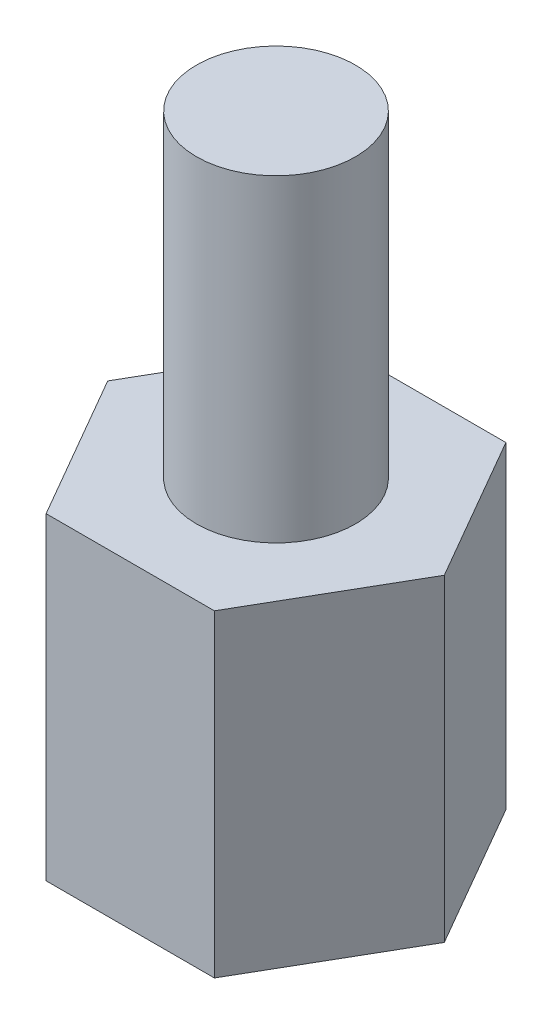
SolidWorks part; units mm, degrees
ref_plane "前视基准面" through (0, 0, 0) normal (0, 0, 1) x (1, 0, 0)
ref_plane "上视基准面" through (0, 0, 0) normal (0, 1, 0) x (1, 0, 0)
ref_plane "右视基准面" through (0, 0, 0) normal (1, 0, 0) x (0, 0, -1)
other "Configuration Table"
sketch "草图1" plane through (0, 0, 0) normal (0, 1, 0) x (1, 0, 0)
  line L1 (3.1754, 0) -> (1.5877, 2.75)
  line L2 (1.5877, 2.75) -> (-1.5877, 2.75)
  line L3 (-1.5877, 2.75) -> (-3.1754, 0)
  line L4 (-3.1754, 0) -> (-1.5877, -2.75)
  line L5 (-1.5877, -2.75) -> (1.5877, -2.75)
  line L6 (1.5877, -2.75) -> (3.1754, 0)
  circle A0 centre (0, 0) radius 2.75 construction
extrude "凸台-拉伸1" add sketch "草图1" along normal blind 6
sketch "草图2" plane through (0, 0, 0) normal (0, -1, 0) x (1, 0, 0)
  circle A0 centre (0, 0) radius 1.5
extrude "切除-拉伸1" cut sketch "草图2" against normal blind 4
sketch "草图3" plane through (0, 6, 0) normal (0, 1, 0) x (1, 0, 0)
  circle A0 centre (0, 0) radius 1.5
extrude "凸台-拉伸2" add sketch "草图3" along normal blind 6
